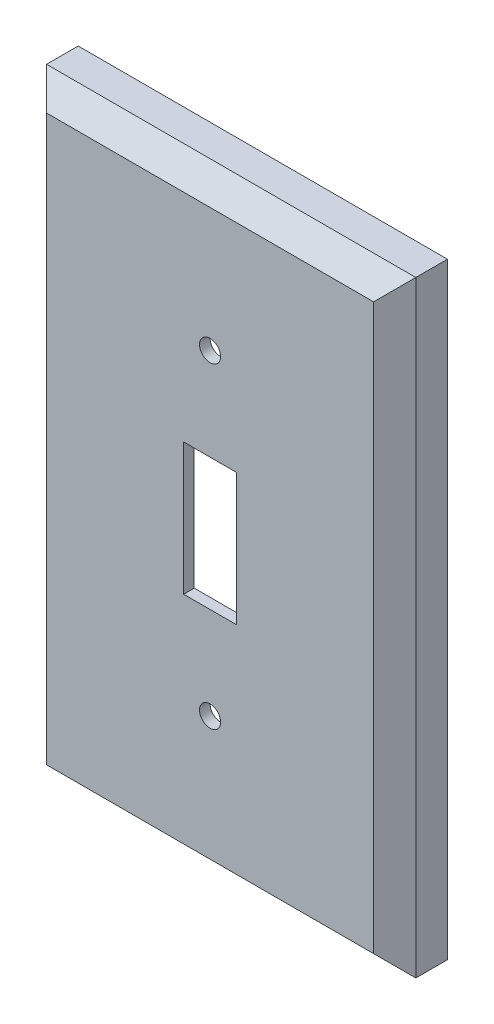
SolidWorks part; units mm, degrees
ref_plane "Front Plane" through (0, 0, 0) normal (0, 0, 1) x (1, 0, 0)
ref_plane "Top Plane" through (0, 0, 0) normal (0, 1, 0) x (1, 0, 0)
ref_plane "Right Plane" through (0, 0, 0) normal (1, 0, 0) x (0, 0, -1)
sketch "Sketch1" plane through (0, 0, 0) normal (0, 1, 0) x (1, 0, 0)
  line L1 (0, 0) -> (70, 0)
  line L2 (0, 0) -> (0, 115)
  line L3 (0, 115) -> (70, 115)
  line L4 (70, 0) -> (70, 115)
  dimension "D1" = 70
  dimension "D2" = 115
extrude "Boss-Extrude1" add sketch "Sketch1" along normal blind 10
sketch3d "3DSketch1"
  line L0 (2, 10, -2) -> (68, 10, -2)
  line L1 (68, 10, -2) -> (68, 10, -113)
  line L2 (68, 10, -113) -> (2, 10, -113)
  line L3 (2, 10, -113) -> (2, 10, -2)
  line L4 (2, 10, -2) -> (68, 10, -2)
  line L5 (68, 10, -2) -> (68, 10, -113)
  line L6 (68, 10, -113) -> (2, 10, -113)
  line L7 (2, 10, -113) -> (2, 10, -2)
  dimension "D1" = 2
extrude "Cut-Extrude1" cut sketch "3DSketch1" along direction (0, -1, 0) on the side of the normal blind 8 contours L4 L5 L6 L7
chamfer "Chamfer1" distance 4 angle 45 4 edges at (35, 0, -115) (0, 0, -57.5) (35, 0, 0) (70, 0, -57.5)
sketch "Sketch2" plane through (0, 2, 0) normal (0, 1, 0) x (1, 0, 0)
  line L0 (70, 0) -> (70, 115) construction
  line L1 (30, 70) -> (40, 70)
  line L2 (30, 70) -> (30, 45)
  line L3 (30, 45) -> (40, 45)
  line L4 (40, 70) -> (40, 45)
  line L5 (70, 115) -> (0, 115) construction
  line L6 (0, 0) -> (70, 0) construction
  circle A0 centre (35, 87.5) radius 2
  circle A1 centre (35, 27.5) radius 2
  dimension "D4" = 4
  dimension "D5" = 4
  dimension "D1" = 60
  dimension "D2" = 25
  dimension "D3" = 10
  dimension "D6" = 35
  dimension "D7" = 35
  dimension "D8" = 30
  dimension "D9" = 45
  dimension "D10" = 27.5
extrude "Cut-Extrude2" cut sketch "Sketch2" against normal blind 8
move or copy body "Body-Move/Copy1" bodies to move or copy 103 copy no rotation origin (0, 5.0001, -57.5) rotation axis (-1, 0, 0) rotation angle 90
equation "\"D10@Sketch2\"=(115-60)/2"
